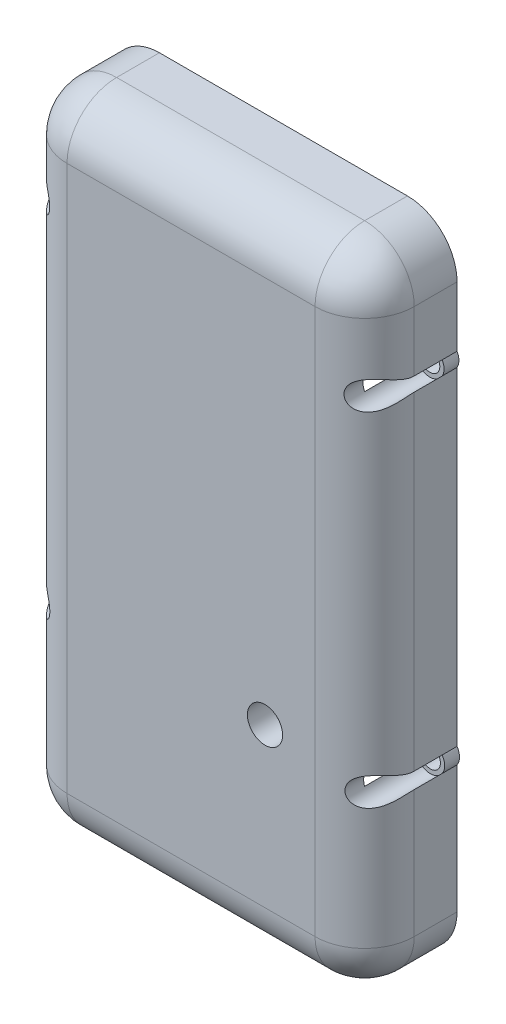
SolidWorks part; units mm, degrees
ref_plane "Front Plane" through (0, 0, 0) normal (0, 0, 1) x (1, 0, 0)
ref_plane "Top Plane" through (0, 0, 0) normal (0, 1, 0) x (1, 0, 0)
ref_plane "Right Plane" through (0, 0, 0) normal (1, 0, 0) x (0, 0, -1)
sketch "Sketch1" plane through (0, 0, 0) normal (0, 0, 1) x (1, 0, 0)
  line L1 (-26.2638, 42.0392) -> (43.7362, 42.0392)
  line L2 (-26.2638, 42.0392) -> (-26.2638, -87.9608)
  line L3 (-26.2638, -87.9608) -> (43.7362, -87.9608)
  line L4 (43.7362, 42.0392) -> (43.7362, -87.9608)
  dimension "D1" = 70
  dimension "D2" = 130
extrude "Boss-Extrude1" add sketch "Sketch1" along normal blind 18.6311
shell "Shell1" thickness 5
fillet "Fillet1" radius 10 1 edges at (-26.2638, -22.9608, 18.6311)
fillet "Fillet2" radius 10 1 edges at (43.7362, -22.9608, 18.6311)
fillet "Fillet4" radius 10 5 edges at (43.7362, 42.0392, 4.3156) (40.8072, 42.0392, 15.7022) (-26.2638, 42.0392, 4.3156) (-23.3349, 42.0392, 15.7022) (8.7362, 42.0392, 18.6311)
fillet "Fillet6" radius 10 5 edges at (-26.2638, -87.9608, 4.3156) (-23.3349, -87.9608, 15.7022) (43.7362, -87.9608, 4.3156) (40.8072, -87.9608, 15.7022) (8.7362, -87.9608, 18.6311)
sketch "Sketch2" plane through (0, 0, 7.7832) normal (0, 0, 1) x (1, 0, 0)
  circle A0 centre (23.6556, -46.034) radius 3.55
extrude "Cut-Extrude1" cut sketch "Sketch2" along normal blind 26 contours A0
sketch "Sketch3" plane through (0, -73.4193, 0) normal (0, -1, 0) x (-1, 0, 0)
  line L1 (1.8182, -9.5516) -> (-12.2922, -9.5516)
  line L2 (1.8182, -9.5516) -> (1.8182, -1.2446)
  line L3 (1.8182, -1.2446) -> (-12.2922, -1.2446)
  line L4 (-12.2922, -9.5516) -> (-12.2922, -1.2446)
extrude "Cut-Extrude4" cut sketch "Sketch3" along normal blind 30 contours L3 L4 L1 L2
sketch "Sketch4" plane through (0, 0, 0) normal (0, 0, 1) x (1, 0, 0)
  circle A0 centre (41.3861, -50.6783) radius 2.85
  circle A1 centre (41.2598, 18.5112) radius 2.85
  circle A2 centre (-23.6935, -49.0424) radius 2.85
  circle A3 centre (-23.7513, 21.5164) radius 2.85
extrude "Cut-Extrude5" cut sketch "Sketch4" along normal blind 24
sketch "Sketch5" plane through (0, 0, 0) normal (0, 0, 1) x (1, 0, 0)
  circle A0 centre (-23.7513, 21.5164) radius 2
  circle A1 centre (41.2598, 18.5112) radius 2
  circle A2 centre (41.3861, -50.6783) radius 2
  circle A3 centre (-23.6935, -49.0424) radius 2
  circle A4 centre (-23.7513, 21.5164) radius 2.85
  circle A5 centre (41.2598, 18.5112) radius 2.85
  circle A6 centre (41.3861, -50.6783) radius 2.85
  circle A7 centre (-23.6935, -49.0424) radius 2.85
extrude "Boss-Extrude2" add sketch "Sketch5" along normal blind 3
